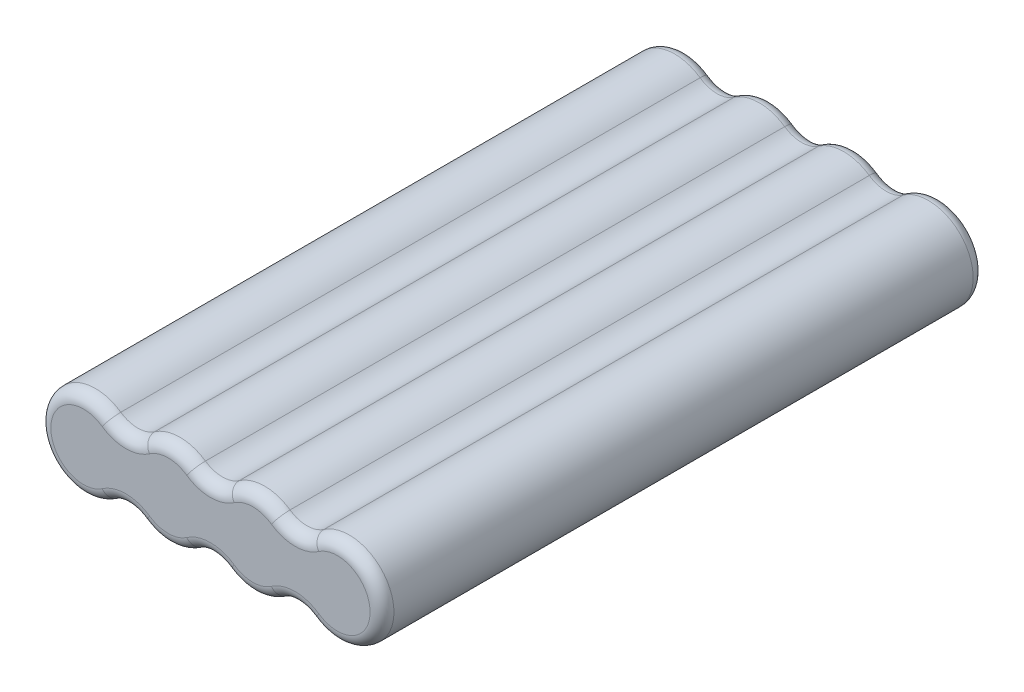
SolidWorks part; units mm, degrees
ref_plane "Front Plane" through (0, 0, 0) normal (0, 0, 1) x (1, 0, 0)
ref_plane "Top Plane" through (0, 0, 0) normal (0, 1, 0) x (1, 0, 0)
ref_plane "Right Plane" through (0, 0, 0) normal (1, 0, 0) x (0, 0, -1)
sketch "Sketch1" plane through (0, 0, 0) normal (0, 0, 1) x (1, 0, 0)
  line L0 (-21.329, 0) -> (-7.1097, 0) construction
  line L1 (-7.1097, 0) -> (7.1097, 0) construction
  line L2 (7.1097, 0) -> (21.329, 0) construction
  arc A0 (-17.0632, 6.1687) -> (-17.0632, -6.1687) centre (-21.329, 0) ccw
  arc A1 (-11.3755, -6.1687) -> (-2.8439, -6.1687) centre (-7.1097, 0) ccw
  arc A2 (2.8439, -6.1687) -> (11.3755, -6.1687) centre (7.1097, 0) ccw
  arc A3 (17.0632, -6.1687) -> (17.0632, 6.1687) centre (21.329, 0) ccw
  arc A4 (-2.8439, 6.1687) -> (-11.3755, 6.1687) centre (-7.1097, 0) ccw
  arc A5 (11.3755, 6.1687) -> (2.8439, 6.1687) centre (7.1097, 0) ccw
  arc A6 (17.0632, -6.1687) -> (11.3755, -6.1687) centre (14.2193, -10.2812) ccw
  arc A7 (2.8439, -6.1687) -> (-2.8439, -6.1687) centre (0, -10.2812) ccw
  arc A8 (-11.3755, -6.1687) -> (-17.0632, -6.1687) centre (-14.2193, -10.2812) ccw
  arc A9 (11.3755, 6.1687) -> (17.0632, 6.1687) centre (14.2193, 10.2812) ccw
  arc A10 (-2.8439, 6.1687) -> (2.8439, 6.1687) centre (0, 10.2812) ccw
  arc A11 (-11.3755, 6.1687) -> (-17.0632, 6.1687) centre (-14.2193, 10.2812) cw
  point P8 (-28.829, 0)
  point P9 (28.829, 0)
  dimension "D1" = 15
  dimension "D3" = 5
  dimension "D2" = 57.658
extrude "Boss-Extrude1" add sketch "Sketch1" along normal mid plane 101.346
fillet "Fillet1" radius 2 24 edges at (28.829, 0, -50.673) (14.2193, 5.2812, -50.673) (7.1097, 7.5, -50.673) (0, 5.2812, -50.673) (-7.1097, 7.5, -50.673) (-14.2193, 5.2812, -50.673) (-28.829, 0, -50.673) (-14.2193, -5.2812, -50.673) (-7.1097, -7.5, -50.673) (0, -5.2812, -50.673) (7.1097, -7.5, -50.673) (14.2193, -5.2812, -50.673) (7.1097, -7.5, 50.673) (0, -5.2812, 50.673) (-7.1097, -7.5, 50.673) (-14.2193, -5.2812, 50.673) (-28.829, 0, 50.673) (-14.2193, 5.2812, 50.673) (-7.1097, 7.5, 50.673) (0, 5.2812, 50.673) (7.1097, 7.5, 50.673) (14.2193, 5.2812, 50.673) (28.829, 0, 50.673) (14.2193, -5.2812, 50.673)
